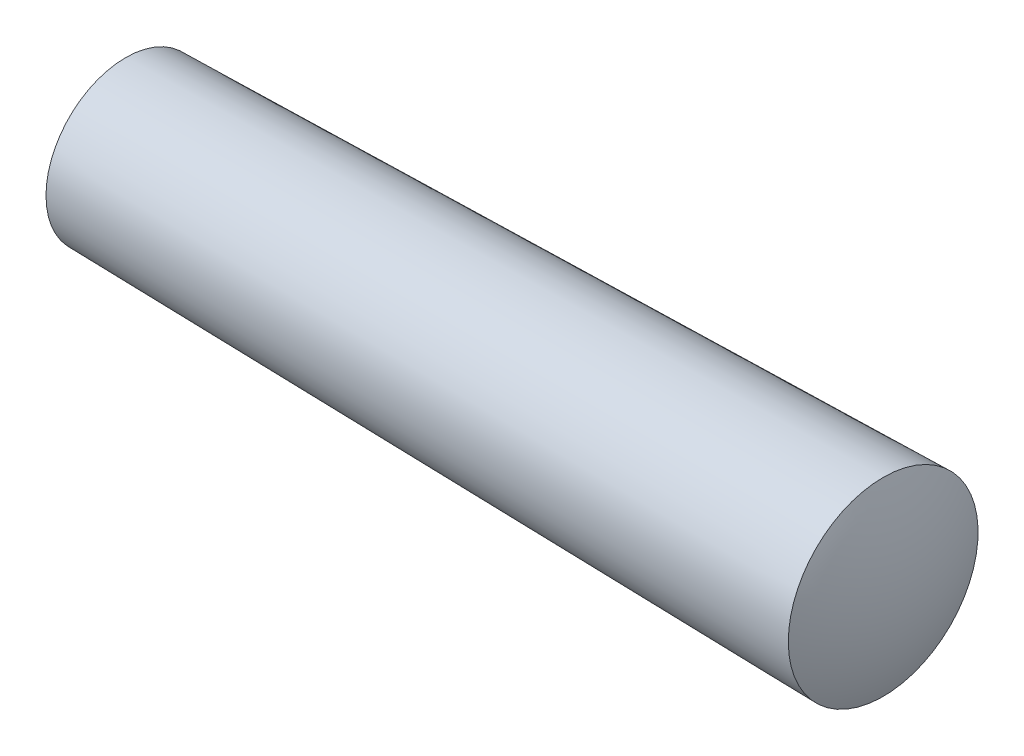
SolidWorks part; units mm, degrees
ref_plane "Front" through (0, 0, 0) normal (0, 0, 1) x (1, 0, 0)
ref_plane "Top" through (0, 0, 0) normal (0, 1, 0) x (1, 0, 0)
ref_plane "Right" through (0, 0, 0) normal (1, 0, 0) x (0, 0, -1)
sketch "Sketch1" plane through (0, 0, 0) normal (0, 0, 1) x (1, 0, 0)
  line L0 (0, 0) -> (40, 0)
  line L1 (1, 4) -> (39, 4) construction
  line L2 (39, 4) -> (39, 4.76) construction
  line L3 (1, 4) -> (39, 4.76)
  line L4 (-4.0035, 0) -> (8.3584, 0) construction
  line L5 (40, 0) -> (40, 2.9125) construction
  line L6 (0, 0) -> (0, -0.8153) construction
  arc A0 (1, 4) -> (0, 0) centre (8.5, 0) ccw
  arc A1 (40, 0) -> (39, 4.76) centre (28.1712, 0) ccw
  dimension "l" = 40
  dimension "D5" = 0.76
  dimension "a" = 1
  dimension "d" = 8
  dimension "a1" = 1
revolve "Base-Revolve" add sketch "Sketch1" angle 360 about L4
ref_plane "基准面1" through (8, 0, 0) normal (1, 0, 0) x (0, 0, -1)
equation "\"D5@Sketch1\" = ( \"l@Sketch1\"-2*\"a@Sketch1\")/ 50"
equation "\"a1@Sketch1\" = \"a@Sketch1\""
